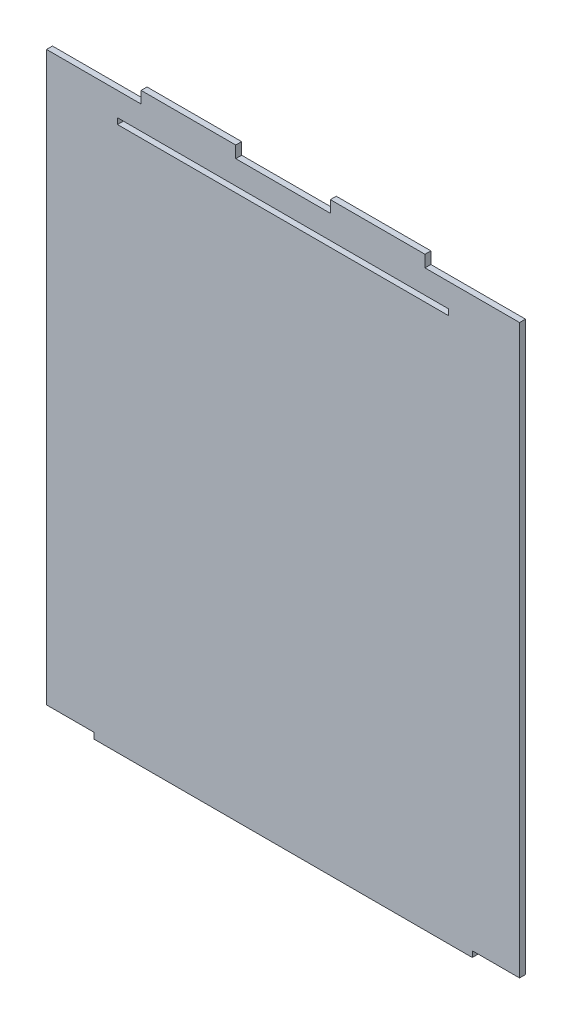
SolidWorks part; units mm, degrees
ref_plane "Front Plane" through (0, 0, 0) normal (0, 0, 1) x (1, 0, 0)
ref_plane "Top Plane" through (0, 0, 0) normal (0, 1, 0) x (1, 0, 0)
ref_plane "Right Plane" through (0, 0, 0) normal (1, 0, 0) x (0, 0, -1)
sketch "Sketch1" plane through (0, 0, 0) normal (0, 0, 1) x (1, 0, 0)
  line L0 (0, -3.175) -> (25.4, -3.175)
  line L1 (25.4, -6.35) -> (228.6, -6.35)
  line L2 (0, -3.175) -> (0, 301.625)
  line L3 (50.8, 307.975) -> (101.6, 307.975)
  line L4 (254, -3.175) -> (254, 301.625)
  line L5 (25.4, -3.175) -> (25.4, -6.35)
  line L6 (25.4, -6.35) -> (228.6, -6.35)
  line L7 (0, 301.625) -> (50.8, 301.625)
  line L8 (50.8, 301.625) -> (50.8, 307.975)
  line L9 (50.8, 307.975) -> (101.6, 307.975)
  line L10 (101.6, 307.975) -> (101.6, 301.625)
  line L11 (101.6, 301.625) -> (152.4, 301.625)
  line L12 (152.4, 301.625) -> (152.4, 307.975)
  line L13 (152.4, 307.975) -> (203.2, 307.975)
  line L14 (203.2, 307.975) -> (203.2, 301.625)
  line L15 (203.2, 301.625) -> (254, 301.625)
  line L16 (152.4, 307.975) -> (203.2, 307.975)
  line L17 (228.6, -6.35) -> (228.6, -3.175)
  line L18 (228.6, -3.175) -> (254, -3.175)
  line L20 (38.1, 288.925) -> (215.9, 288.925)
  line L21 (38.1, 288.925) -> (38.1, 285.75)
  line L22 (38.1, 285.75) -> (215.9, 285.75)
  line L23 (215.9, 288.925) -> (215.9, 285.75)
  dimension "D1" = 314.325
  dimension "D2" = 3.175
  dimension "D3" = 6.35
  dimension "D4" = 50.8
  dimension "D5" = 50.8
  dimension "D6" = 50.8
  dimension "D7" = 50.8
  dimension "D8" = 50.8
  dimension "D9" = 3.175
  dimension "D10" = 25.4
  dimension "D11" = 25.4
  dimension "D12" = 3.175
  dimension "D13" = 177.8
  dimension "D14" = 38.1
  dimension "D15" = 12.7
extrude "Boss-Extrude1" add sketch "Sketch1" along normal blind 3.175 contours L17 L18 L4 L15 L14 L13 L12 L11 L10 L3 L8 L7 L2 L0 L5 L1 L20 L23 L22 L21
